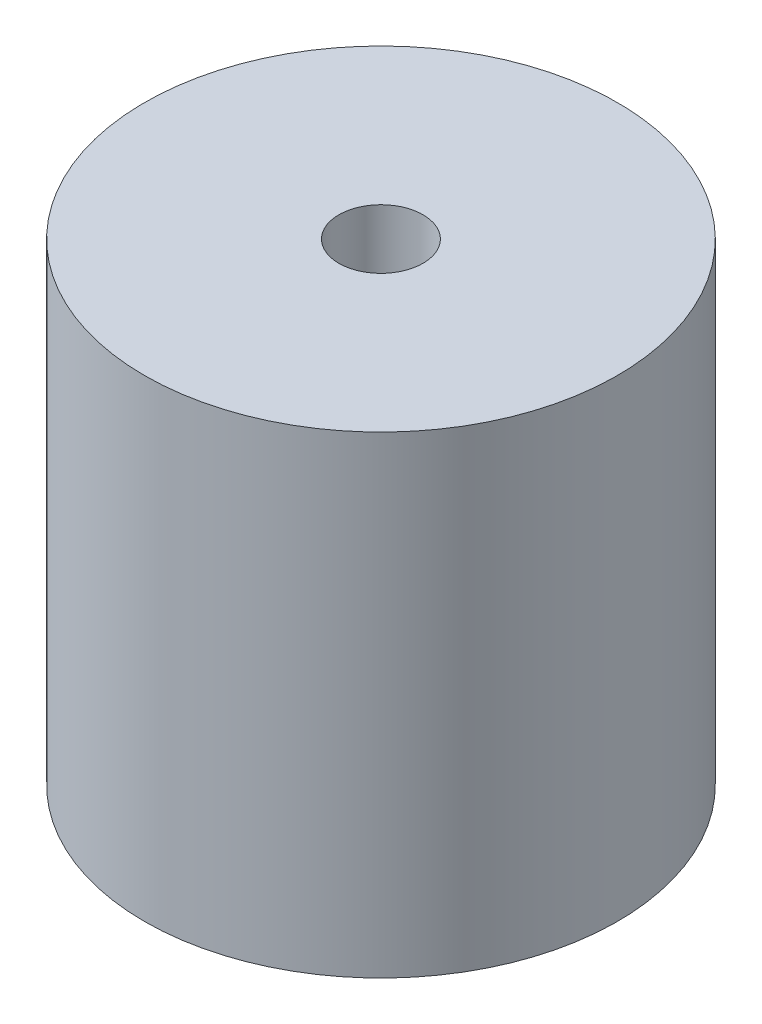
SolidWorks part; units mm, degrees
material "6061-T4 (SS)"
ref_plane "Front Plane" through (0, 0, 0) normal (0, 0, 1) x (1, 0, 0)
ref_plane "Top Plane" through (0, 0, 0) normal (0, 1, 0) x (1, 0, 0)
ref_plane "Right Plane" through (0, 0, 0) normal (1, 0, 0) x (0, 0, -1)
sketch "Sketch1" plane through (0, 0, 0) normal (0, 1, 0) x (1, 0, 0)
  line L0 (0, 0) -> (6.35, 0) construction
  circle A1 centre (0, 0) radius 6.35
  point P1 (-0.0795, 0)
  dimension "D1" = 12.7
extrude "Boss-Extrude1" add sketch "Sketch1" along normal blind 12.7
hole_wizard "#4-40 Tapped Hole1" positions "Sketch2" profile "Sketch4" tap size "#4-40" standard "ANSI Inch"
sketch "Sketch2" plane through (0, 12.7, 0) normal (0, 1, 0) x (1, 0, 0)
  point P0 (0, 0)
sketch "Sketch4" plane through (0, 12.7, 0) normal (1, 0, 0) x (0, 0, 1)
  line L0 (0, 0) -> (0, 4.2352)
  line L1 (0, 4.2352) -> (1.1303, 3.556)
  line L2 (1.1303, 3.556) -> (1.1303, 0)
  line L5 (1.1303, 0) -> (0, 0)
  line L10 (0, 4.2352) -> (-1.1303, 3.556) construction
  line L11 (0, -6.35) -> (0, 107.95) construction
  dimension "Tap Drill Dia." = 2.2606
  dimension "Tap Drill Depth" = 3.556
  dimension "Drill Angle" = 118
cosmetic thread "Hole Thread1" parameters "D1"=5.7, "D2"=2.8448
hole_wizard "1/4-28 Tapped Hole1" positions "Sketch7" profile "Sketch6" tap size "1/4-28" standard "ANSI Inch"
sketch "Sketch7" plane through (0, 0, 0) normal (0, -1, 0) x (-1, 0, 0)
  point P0 (0, 0)
sketch "Sketch6" plane through (0, 0, 0) normal (1, 0, 0) x (0, 0, -1)
  line L0 (0, 0) -> (0, 7.6254)
  line L1 (0, 7.6254) -> (2.7051, 6)
  line L2 (2.7051, 6) -> (2.7051, 0)
  line L5 (2.7051, 0) -> (0, 0)
  line L10 (0, 7.6254) -> (-2.7051, 6) construction
  line L11 (0, -6.35) -> (0, 107.95) construction
  dimension "Tap Drill Dia." = 5.4102
  dimension "Tap Drill Depth" = 6
  dimension "Drill Angle" = 118
cosmetic thread "Hole Thread2"
